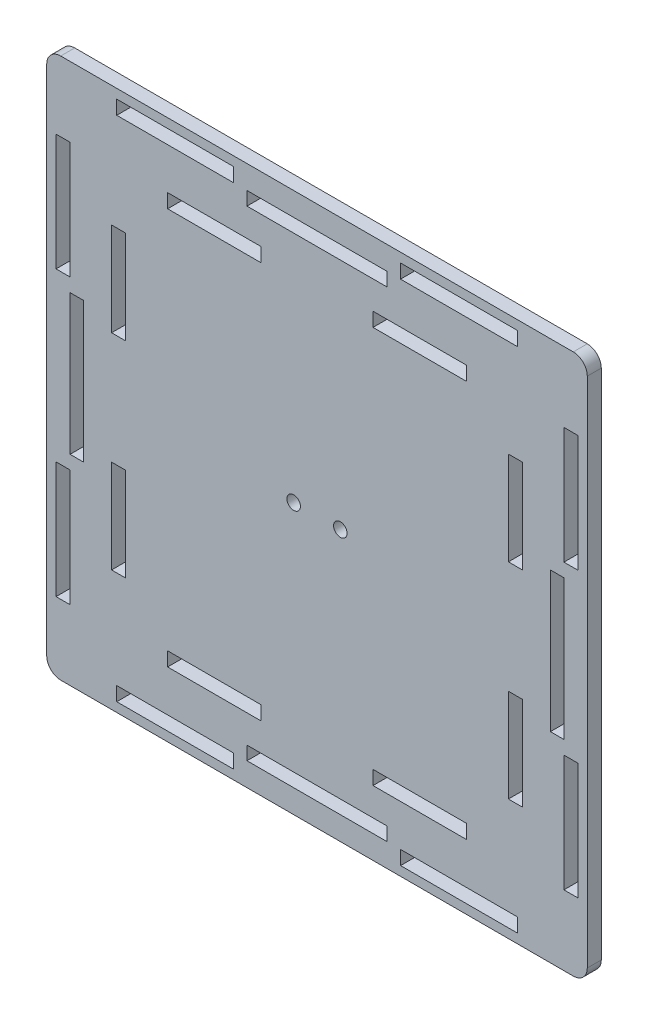
SolidWorks part; units mm, degrees
ref_plane "前视基准面" through (0, 0, 0) normal (0, 0, 1) x (1, 0, 0)
ref_plane "上视基准面" through (0, 0, 0) normal (0, 1, 0) x (1, 0, 0)
ref_plane "右视基准面" through (0, 0, 0) normal (1, 0, 0) x (0, 0, -1)
sketch "草图1" plane through (0, 0, 0) normal (0, 0, 1) x (1, 0, 0)
  line L1 (35, 0) -> (65, 0)
  line L2 (0, 35) -> (0, 65)
  line L3 (35, 100) -> (65, 100)
  line L4 (100, 35) -> (100, 65)
  line L6 (67.9, 102.9) -> (92.9, 102.9)
  line L7 (18, 94) -> (38, 94)
  line L8 (6, 82) -> (6, 62)
  line L9 (18, 6) -> (38, 6)
  line L10 (94, 82) -> (94, 62)
  line L12 (40, 55) -> (60, 55)
  line L13 (7.1, 102.9) -> (32.1, 102.9)
  line L14 (-2.9, 92.9) -> (-2.9, 67.9)
  line L15 (7.1, -2.9) -> (32.1, -2.9)
  line L16 (102.9, 92.9) -> (102.9, 67.9)
  line L17 (40, 55) -> (40, 45)
  line L18 (40, 45) -> (60, 45)
  line L19 (-4.9, 107.9) -> (104.9, 107.9)
  line L20 (-7.9, 104.9) -> (-7.9, -4.9)
  line L21 (-4.9, -7.9) -> (104.9, -7.9)
  line L22 (107.9, 104.9) -> (107.9, -4.9)
  line L23 (60, 55) -> (60, 45)
  line L25 (35, 102.9) -> (65, 102.9)
  line L26 (102.9, 92.9) -> (105.9, 92.9)
  line L27 (102.9, 92.9) -> (102.9, 67.9)
  line L28 (102.9, 67.9) -> (105.9, 67.9)
  line L29 (105.9, 92.9) -> (105.9, 67.9)
  line L30 (102.9, 32.1) -> (102.9, 7.1)
  line L31 (92.9, 102.9) -> (67.9, 102.9)
  line L32 (92.9, 102.9) -> (92.9, 105.9)
  line L33 (92.9, 105.9) -> (67.9, 105.9)
  line L34 (67.9, 102.9) -> (67.9, 105.9)
  line L35 (102.9, 65) -> (102.9, 35)
  line L36 (102.9, 7.1) -> (105.9, 7.1)
  line L37 (102.9, 7.1) -> (102.9, 32.1)
  line L38 (102.9, 32.1) -> (105.9, 32.1)
  line L39 (105.9, 7.1) -> (105.9, 32.1)
  line L40 (35, -2.9) -> (65, -2.9)
  line L41 (92.9, -2.9) -> (67.9, -2.9)
  line L42 (92.9, -2.9) -> (92.9, -5.9)
  line L43 (92.9, -5.9) -> (67.9, -5.9)
  line L44 (67.9, -2.9) -> (67.9, -5.9)
  line L45 (67.9, -2.9) -> (92.9, -2.9)
  line L46 (7.1, -2.9) -> (32.1, -2.9)
  line L47 (7.1, -2.9) -> (7.1, -5.9)
  line L48 (7.1, -5.9) -> (32.1, -5.9)
  line L49 (32.1, -2.9) -> (32.1, -5.9)
  line L50 (-2.9, 32.1) -> (-2.9, 7.1)
  line L51 (-2.9, 7.1) -> (-5.9, 7.1)
  line L52 (-2.9, 7.1) -> (-2.9, 32.1)
  line L53 (-2.9, 32.1) -> (-5.9, 32.1)
  line L54 (-5.9, 7.1) -> (-5.9, 32.1)
  line L55 (-2.9, 65) -> (-2.9, 35)
  line L56 (-2.9, 92.9) -> (-5.9, 92.9)
  line L57 (-2.9, 92.9) -> (-2.9, 67.9)
  line L58 (-2.9, 67.9) -> (-5.9, 67.9)
  line L59 (-5.9, 92.9) -> (-5.9, 67.9)
  line L60 (102.9, 35) -> (102.9, 65)
  line L61 (7.1, 102.9) -> (32.1, 102.9)
  line L62 (7.1, 102.9) -> (7.1, 105.9)
  line L63 (7.1, 105.9) -> (32.1, 105.9)
  line L64 (32.1, 102.9) -> (32.1, 105.9)
  line L65 (35, -2.9) -> (65, -2.9)
  line L66 (102.9, 35) -> (100, 35)
  line L67 (102.9, 35) -> (102.9, 65)
  line L68 (102.9, 65) -> (100, 65)
  line L69 (100, 35) -> (100, 65)
  line L70 (-2.9, 65) -> (-2.9, 35)
  line L71 (35, -2.9) -> (65, -2.9)
  line L72 (35, -2.9) -> (35, 0)
  line L73 (35, 0) -> (65, 0)
  line L74 (65, -2.9) -> (65, 0)
  line L75 (35, 102.9) -> (65, 102.9)
  line L76 (-2.9, 65) -> (0, 65)
  line L77 (-2.9, 65) -> (-2.9, 35)
  line L78 (-2.9, 35) -> (0, 35)
  line L79 (0, 65) -> (0, 35)
  line L80 (18, 94) -> (38, 94)
  line L81 (35, 102.9) -> (65, 102.9)
  line L82 (35, 102.9) -> (35, 100)
  line L83 (35, 100) -> (65, 100)
  line L84 (65, 102.9) -> (65, 100)
  line L85 (62, 94) -> (82, 94)
  line L86 (28, 94) -> (38, 94)
  line L90 (28, 94) -> (18, 94)
  line L94 (62, 94) -> (82, 94)
  line L95 (94, 82) -> (94, 62)
  line L96 (72, 94) -> (82, 94)
  line L100 (72, 94) -> (62, 94)
  line L104 (18, 94) -> (38, 94)
  line L105 (18, 94) -> (18, 91)
  line L106 (18, 91) -> (38, 91)
  line L107 (38, 94) -> (38, 91)
  line L108 (62, 94) -> (82, 94)
  line L109 (62, 94) -> (62, 91)
  line L110 (62, 91) -> (82, 91)
  line L111 (82, 94) -> (82, 91)
  line L112 (94, 82) -> (94, 72)
  line L113 (6, 38) -> (6, 18)
  line L115 (18, 9) -> (18, 6)
  line L116 (62, 6) -> (82, 6)
  line L117 (62, 6) -> (62, 9)
  line L118 (62, 9) -> (82, 9)
  line L119 (82, 6) -> (82, 9)
  line L120 (38, 9) -> (38, 6)
  line L121 (62, 9) -> (62, 6)
  line L122 (38, 6) -> (18, 6)
  line L123 (38, 6) -> (38, 9)
  line L124 (38, 9) -> (18, 9)
  line L125 (18, 6) -> (18, 9)
  line L126 (82, 9) -> (82, 6)
  line L127 (6, 72) -> (6, 82)
  line L128 (6, 82) -> (9, 82)
  line L129 (9, 72) -> (9, 82)
  line L131 (6, 72) -> (6, 62)
  line L132 (6, 62) -> (9, 62)
  line L133 (9, 72) -> (9, 62)
  line L134 (91, 62) -> (94, 62)
  line L136 (6, 28) -> (6, 38)
  line L137 (6, 38) -> (9, 38)
  line L138 (9, 28) -> (9, 38)
  line L140 (6, 28) -> (6, 18)
  line L141 (6, 18) -> (9, 18)
  line L142 (9, 28) -> (9, 18)
  line L143 (91, 18) -> (94, 18)
  line L144 (62, 6) -> (82, 6)
  line L145 (91, 38) -> (94, 38)
  line L146 (91, 82) -> (94, 82)
  line L147 (94, 18) -> (91, 18)
  line L148 (94, 18) -> (94, 38)
  line L149 (94, 38) -> (91, 38)
  line L150 (91, 18) -> (91, 38)
  line L151 (94, 62) -> (91, 62)
  line L152 (94, 62) -> (94, 82)
  line L153 (94, 82) -> (91, 82)
  line L154 (91, 62) -> (91, 82)
  line L155 (94, 38) -> (94, 18)
  line L156 (62, 94) -> (82, 94)
  line L157 (6, 38) -> (6, 18)
  line L159 (6, 6) -> (94, 6) construction
  line L160 (6, 6) -> (6, 94) construction
  line L161 (6, 94) -> (94, 94) construction
  line L162 (94, 6) -> (94, 94) construction
  line L165 (0, 0) -> (100, 0) construction
  line L166 (0, 0) -> (0, 100) construction
  line L167 (0, 100) -> (100, 100) construction
  line L168 (100, 0) -> (100, 100) construction
  line L171 (102.9, -2.9) -> (-2.9, -2.9) construction
  line L172 (102.9, -2.9) -> (102.9, 102.9) construction
  line L173 (102.9, 102.9) -> (-2.9, 102.9) construction
  line L174 (-2.9, -2.9) -> (-2.9, 102.9) construction
  circle A0 centre (55, 50) radius 1.45
  circle A1 centre (45, 50) radius 1.45
  arc A2 (104.9, -7.9) -> (107.9, -4.9) centre (104.9, -4.9) ccw
  arc A3 (-4.9, -7.9) -> (-7.9, -4.9) centre (-4.9, -4.9) cw
  arc A4 (-7.9, 104.9) -> (-4.9, 107.9) centre (-4.9, 104.9) cw
  arc A5 (107.9, 104.9) -> (104.9, 107.9) centre (104.9, 104.9) ccw
  point P9 (50, 50)
  point P10 (50, 50)
  point P14 (50, 50)
  point P19 (50, 50)
  point P59 (102.9, 50)
  point P62 (50, 50)
  point P65 (50, -2.9)
  point P71 (-2.9, 50)
  point P77 (50, 102.9)
  point P118 (50, 50)
  point P119 (50, 50)
  point P127 (50, 50)
extrude "凸台-拉伸2" add sketch "草图1" along normal blind 3 contours L22 L19 L20 L21 L124 L120 L9 L115 L119 L116 L117 L118 L78 L55 L76 L2 L74 L40 L72 L1 L68 L35 L66 L4 L64 L13 L62 L63 L59 L56 L14 L58 L44 L41 L42 L43 L39 L36 L30 L38 L12 | L23 L12 L17 L18 A1 A0
